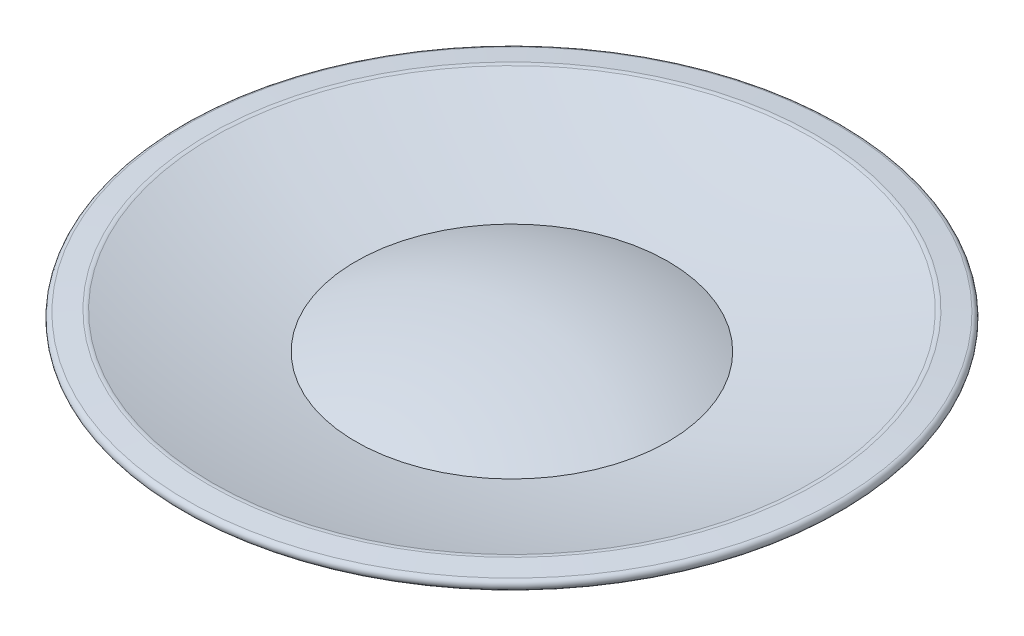
SolidWorks part; units mm, degrees
material "A-Glass Fiber"
ref_plane "Front Plane" through (0, 0, 0) normal (0, 0, 1) x (1, 0, 0)
ref_plane "Top Plane" through (0, 0, 0) normal (0, 1, 0) x (1, 0, 0)
ref_plane "Right Plane" through (0, 0, 0) normal (1, 0, 0) x (0, 0, -1)
sketch "Sketch1" plane through (0, 0, 0) normal (0, 0, 1) x (1, 0, 0)
  line L0 (-1.5, 0) -> (-1.5, 1.25)
  line L1 (0, 0) -> (0, 3.177) construction
  line L2 (-1.5, 0) -> (-1.4375, 0)
  line L3 (-3.9417, 2.0637) -> (-4.2266, 2.0312)
  line L4 (-1.25, 0) -> (-1.25, 1.4669) construction
  line L5 (-1.4375, 0) -> (-1.4375, 1)
  line L6 (-1.4375, 1) -> (0, 1)
  line L7 (0, 2) -> (0, 1)
  arc A0 (0, 2) -> (-2.0286, 1.5922) centre (0, -3.25) ccw
  arc A1 (-1.5, 1.25) -> (-4.2395, 1.9098) centre (0.8624, 17.0746) cw
  arc A2 (-2.0286, 1.5922) -> (-3.8898, 2.0587) centre (0.8624, 17.0746) cw
  arc A3 (-1.25, 1.4669) -> (-3.904, 2.0632) centre (0.8624, 17.0746) cw construction
  arc A4 (-3.9417, 2.0637) -> (-3.8898, 2.0587) centre (-3.9275, 1.9395) cw
  arc A5 (-1.5, 1.25) -> (-3.9797, 1.8249) centre (0.8624, 17.0746) cw construction
  arc A6 (-4.2266, 2.0312) -> (-4.2395, 1.9098) centre (-4.2196, 1.9691) ccw
  point P19 (-4.5, 2)
  dimension "D3" = 10.5
  dimension "D7" = 16
  dimension "D9" = 0.125
  dimension "D10" = 0.0625
  dimension "D1" = 1.5
  dimension "D2" = 1.25
  dimension "D4" = 3.25
  dimension "D5" = 4.5
  dimension "D6" = 0.75
  dimension "D11" = 4.8041
  dimension "D12" = 0.0625
  dimension "D13" = 1
  dimension "D8" = 0.25
revolve "Revolve1" add sketch "Sketch1" angle 360 about L1
